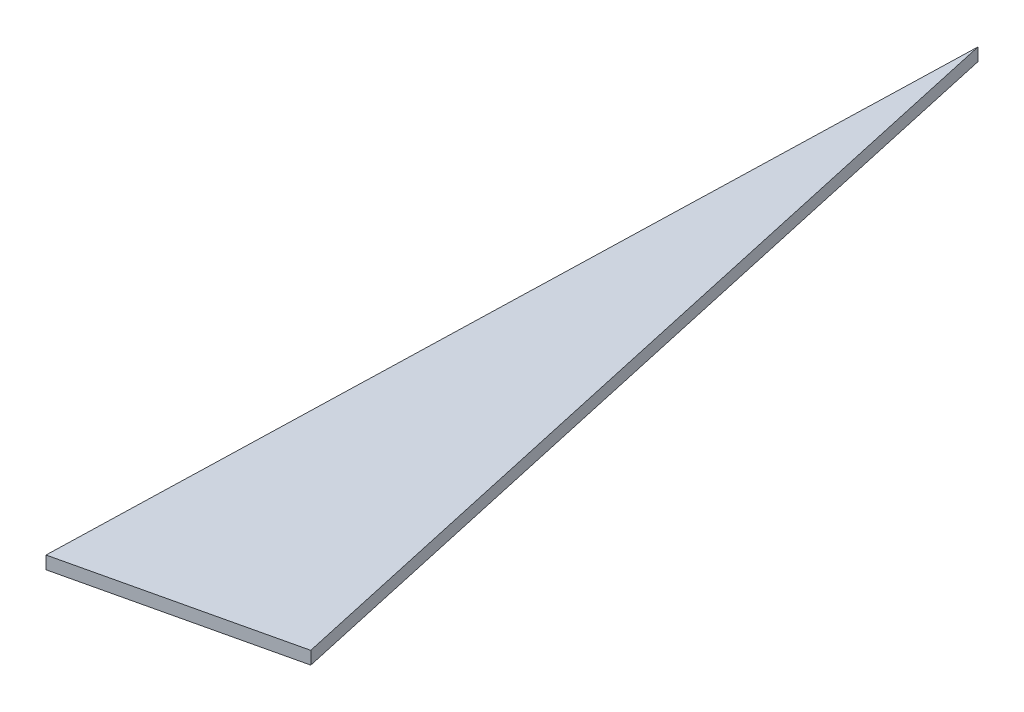
SolidWorks part; units mm, degrees
ref_plane "Plan de face" through (0, 0, 0) normal (0, 0, 1) x (1, 0, 0)
ref_plane "Plan de dessus" through (0, 0, 0) normal (0, 1, 0) x (1, 0, 0)
ref_plane "Plan de droite" through (0, 0, 0) normal (1, 0, 0) x (0, 0, -1)
sketch "Esquisse1" plane through (0, 0, 0) normal (0, 1, 0) x (1, 0, 0)
  line L0 (33.5515, 7.7742) -> (4.0521, 141.4141)
  line L1 (4.0521, 141.4141) -> (0, 0)
  line L2 (0, 0) -> (33.5515, 7.7742)
  point P3 (0, 0)
extrude "Boss.-Extru.1" add sketch "Esquisse1" along normal blind 2
